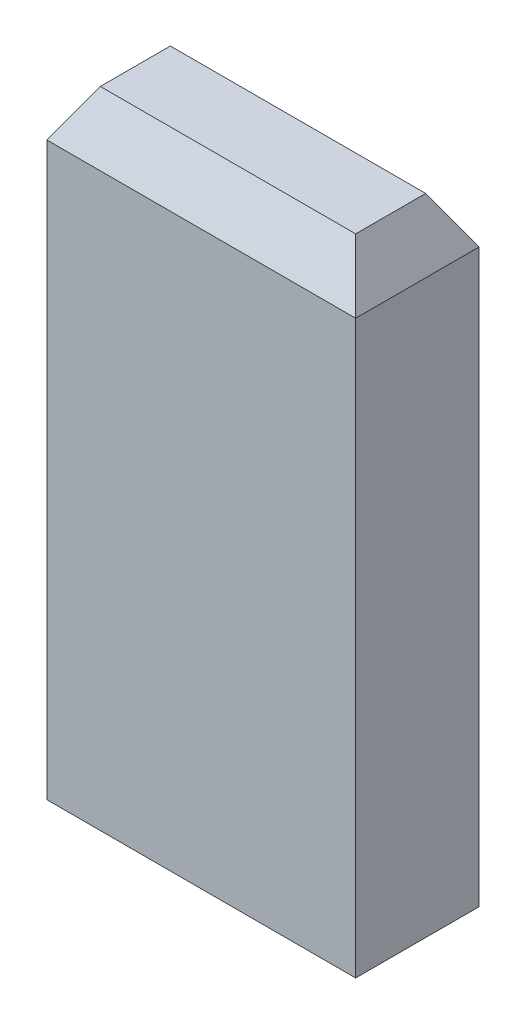
SolidWorks part; units mm, degrees
material "Brass"
ref_plane "Front Plane" through (0, 0, 0) normal (0, 0, 1) x (1, 0, 0)
ref_plane "Top Plane" through (0, 0, 0) normal (0, 1, 0) x (1, 0, 0)
ref_plane "Right Plane" through (0, 0, 0) normal (1, 0, 0) x (0, 0, -1)
sketch "Sketch1" plane through (0, 0, 0) normal (0, 1, 0) x (-1, 0, 0)
  line L1 (0, 0) -> (2, 0)
  line L2 (0, 0) -> (0, -0.8)
  line L3 (0, -0.8) -> (2, -0.8)
  line L4 (2, 0) -> (2, -0.8)
  dimension "D1" = 2
  dimension "D2" = 0.8
extrude "Boss-Extrude1" add sketch "Sketch1" along normal blind 4
chamfer "Chamfer1" distance 0.3 angle 30 4 edges at (-1, 4, 0) (-2, 4, -0.4) (-1, 4, -0.8) (0, 4, -0.4)
